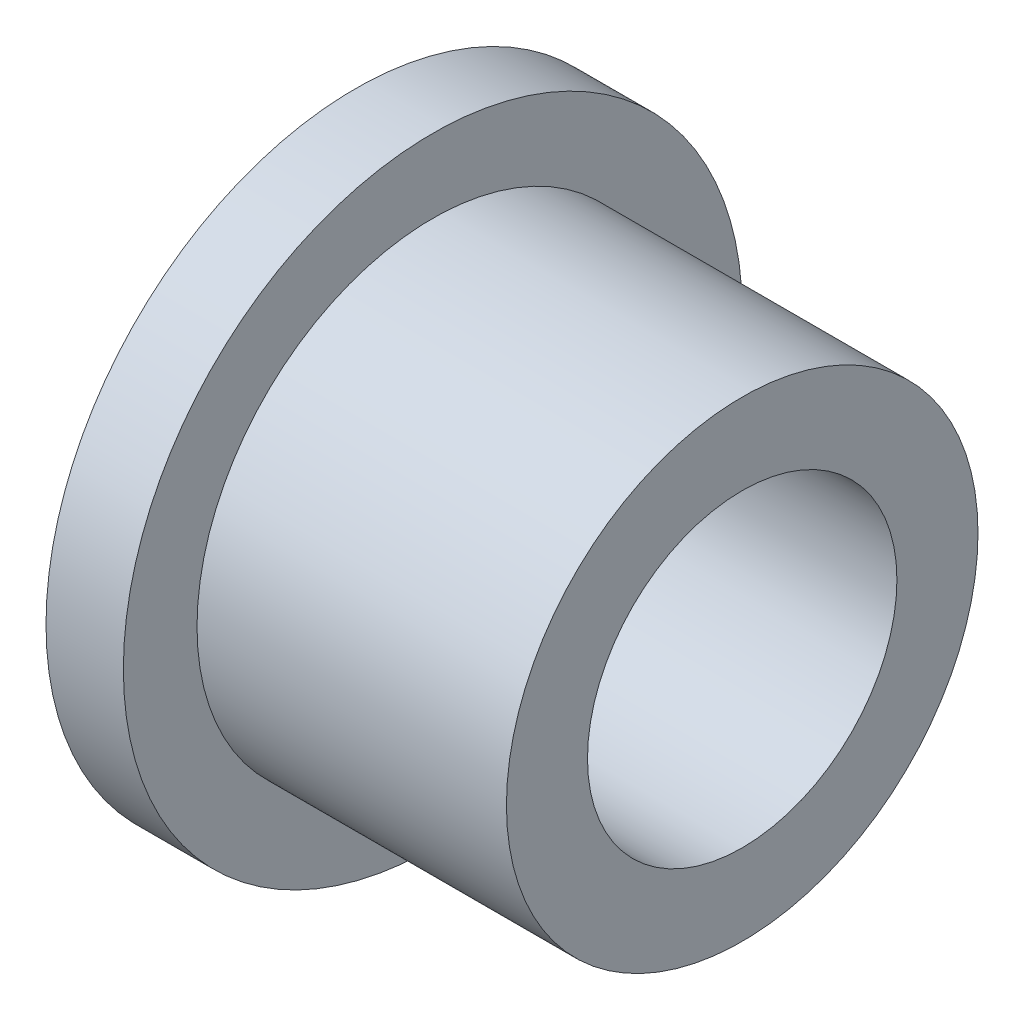
SolidWorks part; units mm, degrees
material "Brass"
ref_plane "Front Plane" through (0, 0, 0) normal (0, 0, 1) x (1, 0, 0)
ref_plane "Top Plane" through (0, 0, 0) normal (0, 1, 0) x (1, 0, 0)
ref_plane "Right Plane" through (0, 0, 0) normal (1, 0, 0) x (0, 0, -1)
sketch "Sketch1" plane through (0, 0, 0) normal (1, 0, 0) x (0, 0, -1)
  circle A0 centre (0, 0) radius 3.175
  circle A1 centre (0, 0) radius 6.35
  dimension "D1" = 6.35
  dimension "D2" = 12.7
extrude "Boss-Extrude1" add sketch "Sketch1" along normal blind 1.5875
sketch "Sketch2" plane through (1.5875, 0, 0) normal (1, 0, 0) x (0, 0, -1)
  circle A0 centre (0, 0) radius 3.175
  circle A1 centre (0, 0) radius 4.8387
  circle A2 centre (0, 0) radius 3.175 construction
  dimension "D1" = 9.6774
extrude "Boss-Extrude2" add sketch "Sketch2" along normal blind 6.35
